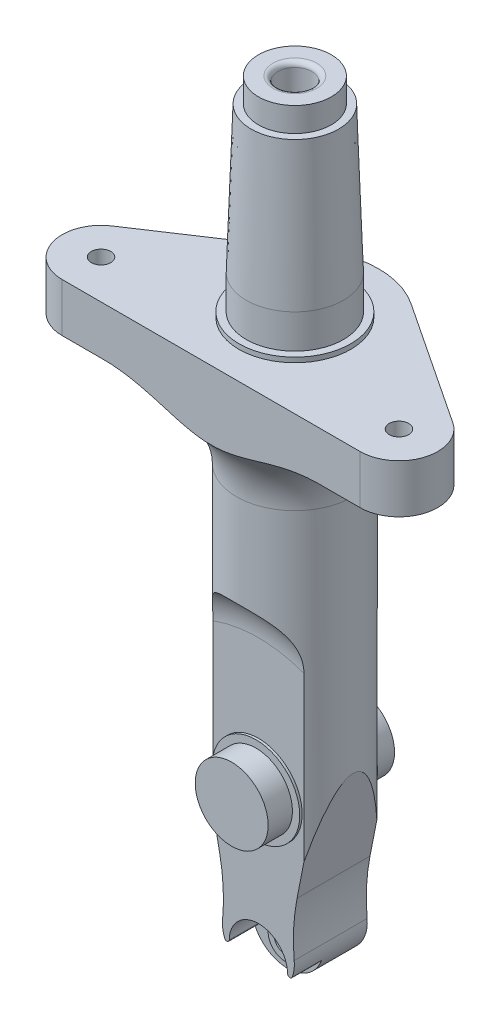
SolidWorks part; units mm, degrees
ref_plane "Front Plane" through (0, 0, 0) normal (0, 0, 1) x (1, 0, 0)
ref_plane "Top Plane" through (0, 0, 0) normal (0, 1, 0) x (1, 0, 0)
ref_plane "Right Plane" through (0, 0, 0) normal (1, 0, 0) x (0, 0, -1)
sketch "Sketch1" plane through (0, 0, 0) normal (1, 0, 0) x (0, 0, -1)
  line L0 (0, 0) -> (-12, 0)
  line L1 (-12, 0) -> (-12, 88.2723)
  line L2 (-12, 88.2723) -> (0, 88.2723)
  line L3 (0, 88.2723) -> (0, 0)
  dimension "D1" = 12
revolve "Revolve1" add sketch "Sketch1" angle 360 about L3
sketch "Sketch2" plane through (0, 0, 0) normal (1, 0, 0) x (0, 0, -1)
  line L0 (0, 0) -> (0, 42.6195) construction
  line L5 (-12, 88.2723) -> (-12, 0) construction
  line L6 (-12, 0) -> (-7.5, 0)
  line L7 (-12, 0) -> (12, 0) construction
  line L8 (-12, 0) -> (-12, 60)
  line L9 (-12, 60) -> (-7.5, 60)
  line L10 (-7.5, 0) -> (-7.5, 60)
  line L11 (7.5, 0) -> (7.5, 60)
  line L12 (12, 60) -> (7.5, 60)
  line L13 (12, 0) -> (12, 60)
  line L14 (12, 0) -> (7.5, 0)
  dimension "D1" = 7.5
  dimension "D2" = 60
extrude "Cut-Extrude1" cut sketch "Sketch2" against normal through all both and the other way through all
sketch "Sketch3" plane through (0, 0, 7.5) normal (0, 0, 1) x (1, 0, 0)
  line L0 (-9.3675, 0) -> (9.3675, 0) construction
  line L1 (0, 5) -> (0, 0) construction
  line L2 (-12, 40) -> (12, 40) construction
  line L3 (-12, 88.2723) -> (-12, 0) construction
  line L4 (12, 0) -> (12, 88.2723) construction
  line L5 (-12, 40) -> (-4.9055, 4.0324)
  line L6 (12, 40) -> (4.9055, 4.0324)
  line L7 (-12, 40) -> (-12, 0)
  line L9 (12, 0) -> (12, 40)
  line L10 (-12, 0) -> (-12, -1)
  line L11 (-12, -1) -> (12, -1)
  line L12 (12, -1) -> (12, 0)
  arc A0 (-4.9055, 4.0324) -> (4.9055, 4.0324) centre (0, 5) ccw
  dimension "D1" = 10
  dimension "D2" = 40
  dimension "D3" = 1
extrude "Cut-Extrude2" cut sketch "Sketch3" against normal through all both and the other way through all
sketch "Sketch12" plane through (0, 0, 7.5) normal (0, 0, 1) x (1, 0, 0)
  circle A0 centre (0, 7.3939) radius 7.3939
extrude "Boss-Extrude4" add sketch "Sketch12" against normal up to surface (15 mm away) up to face at (0, 29.5567, -7.5)
fillet "Fillet2" radius 40 2 edges at (-6.3241, 11.2247, 0) (6.3241, 11.2247, 0)
sketch "Sketch4" plane through (0, 0, 7.5) normal (0, 0, 1) x (1, 0, 0)
  line L0 (0, 5) -> (0, 0) construction
  circle A0 centre (0, 5) radius 6
  dimension "D1" = 12
  dimension "D2" = 5
extrude "Cut-Extrude3" cut sketch "Sketch4" against normal blind 6
sketch "Sketch5" plane through (0, 0, 1.5) normal (0, 0, 1) x (1, 0, 0)
  line L0 (0, 5) -> (0, 0) construction
  circle A0 centre (0, 5) radius 2.25
  dimension "D1" = 4.5
  dimension "D2" = 5
extrude "Cut-Extrude4" cut sketch "Sketch5" against normal through all
sketch "Sketch6" plane through (0, 0, 0) normal (0, 0, 1) x (1, 0, 0)
  line L0 (0, 35) -> (0, 5) construction
  circle A0 centre (0, 35) radius 7.5
  dimension "D1" = 15
  dimension "D2" = 30
extrude "Boss-Extrude1" add sketch "Sketch6" along normal mid plane 26
sketch "Sketch7" plane through (0, 0, 0) normal (1, 0, 0) x (0, 0, -1)
  line L0 (-43.1434, 61.9274) -> (-20.4641, 61.9274) construction
  line L5 (0, 88.2723) -> (0, 0) construction
  line L6 (12, 88.2723) -> (-12, 88.2723) construction
  line L7 (-7.5, 26.6538) -> (-7.5, 60) construction
  line L8 (-7.5, 61.9274) -> (-7.5, 51.9274)
  line L11 (-13, 35) -> (13, 35) construction
  line L12 (-13, 42.5) -> (-13, 27.5) construction
  line L13 (13, 27.5) -> (13, 42.5) construction
  line L16 (-7.5, 51.9274) -> (-17.5, 51.9274)
  line L17 (7.5, 51.9274) -> (17.5, 51.9274)
  line L18 (7.5, 61.9274) -> (7.5, 51.9274)
  arc A2 (-7.5, 61.9274) -> (-17.5, 51.9274) centre (-17.5, 61.9274) ccw
  arc A4 (7.5, 61.9274) -> (17.5, 51.9274) centre (17.5, 61.9274) cw
  point P9 (-7.5, 61.9274)
  point P27 (7.5, 61.9274)
  dimension "D1" = 20
revolve "Cut-Revolve1" cut sketch "Sketch7" angle 360 about L11
sketch "Sketch8" plane through (0, 0, 0) normal (1, 0, 0) x (0, 0, -1)
  line L0 (0, 88.2723) -> (0, 25.4203)
  line L1 (12, 88.2723) -> (-12, 88.2723) construction
  arc A0 (0, 25.4203) -> (12.8128, 10.5806) centre (15, 25.4203) ccw
  dimension "D1" = 30
sketch "Sketch9" plane through (0, 88.2723, 0) normal (0, 1, 0) x (1, 0, 0)
  circle A0 centre (0, 0) radius 3.5
  dimension "D1" = 7
sweep "Cut-Sweep1" cut profiles "Sketch9" path "Sketch8"
sketch "Sketch10" plane through (0, 0, 0) normal (0, 0, 1) x (1, 0, 0)
  circle A0 centre (0, 35) radius 9
  dimension "D1" = 18
extrude "Boss-Extrude2" add sketch "Sketch10" along normal mid plane 16
sketch "Sketch11" plane through (0, 0, 1.5) normal (0, 0, 1) x (1, 0, 0)
  circle A0 centre (0, 5) radius 2.25 construction
  circle A1 centre (0, 5) radius 2.25
  circle A2 centre (0, 5) radius 3.5
  dimension "D1" = 7
extrude "Boss-Extrude3" add sketch "Sketch11" along normal blind 0.5
fillet "Fillet1" radius 0.5 2 edges at (5.3569, 2.2975, 4.5) (-5.3569, 2.2975, 4.5)
sketch "Sketch13" plane through (0, 88.2723, 0) normal (0, 1, 0) x (1, 0, 0)
  circle A0 centre (0, 0) radius 3.5 construction
  circle A1 centre (0, 0) radius 12
  circle A2 centre (0, 0) radius 12
  circle A3 centre (0, 0) radius 3.5
  dimension "D1" = 0
extrude "Boss-Extrude5" add sketch "Sketch13" along normal blind 17
sketch "Sketch15" plane through (0, 0, 0) normal (1, 0, 0) x (0, 0, -1)
  line L0 (-13, 35) -> (13, 35) construction
  line L1 (-13, 42.5) -> (-13, 27.5) construction
  line L2 (13, 27.5) -> (13, 42.5) construction
  line L3 (0, 88.826) -> (0, 43.2314) construction
  line L4 (12, 105.2723) -> (-12, 105.2723) construction
  line L5 (0, 105.2723) -> (-40, 105.2723)
  line L6 (0, 105.2723) -> (0, 123.2723)
  line L8 (-40, 105.2723) -> (-40, 115.2723)
  line L9 (-11.5, 115.2723) -> (-40, 115.2723)
  line L12 (0, 123.2723) -> (-10, 123.2723)
  line L13 (-10, 116.2723) -> (-10, 123.2723)
  line L16 (-10, 116.2723) -> (-11.5, 116.2723)
  line L17 (-11.5, 115.2723) -> (-11.5, 116.2723)
  dimension "D1" = 40
  dimension "D2" = 10
  dimension "D3" = 10
  dimension "D4" = 7
  dimension "D5" = 1
  dimension "D6" = 1.5
revolve "Revolve2" add sketch "Sketch15" angle 360 about L3
fillet "Fillet3" radius 16 1 edges at (0, 105.2723, 12)
sketch "Sketch16" plane through (0, 115.2723, 0) normal (0, 1, 0) x (1, 0, 0)
  line L0 (-30.6386, -9.2345) -> (0, 0) construction
  line L1 (0, 0) -> (38.2982, -11.5432) construction
  line L2 (0, 0) -> (0, -40) construction
  line L3 (-30.6386, -17.2345) -> (30.6386, -17.2345)
  line L4 (-35.0594, -2.567) -> (-9.5239, 14.364)
  line L5 (9.5239, 14.364) -> (35.0594, -2.567)
  arc A0 (-35.0594, -2.567) -> (-30.6386, -17.2345) centre (-30.6386, -9.2345) ccw
  circle A1 centre (0, 0) radius 40 construction
  arc A2 (30.6386, -17.2345) -> (35.0594, -2.567) centre (30.6386, -9.2345) ccw
  arc A4 (9.5239, 14.364) -> (-9.5239, 14.364) centre (0, 0) ccw
  circle A6 centre (0, 0) radius 77.6503
  circle A9 centre (0, 0) radius 17.2345 construction
  dimension "D2" = 8
  dimension "D1" = 34.4691
extrude "Cut-Extrude5" cut sketch "Sketch16" against normal blind 22
sketch "Sketch17" plane through (0, 115.2723, 0) normal (0, 1, 0) x (1, 0, 0)
  circle A0 centre (-30.6386, -9.2345) radius 2
  circle A1 centre (30.6386, -9.2345) radius 2
  dimension "D1" = 4
extrude "Cut-Extrude6" cut sketch "Sketch17" against normal blind 22
sketch "Sketch19" plane through (0, 0, 0) normal (0, 0, 1) x (1, 0, 0)
  line L0 (0, 123.2723) -> (0, 158.2723) construction
  line L1 (10, 123.2723) -> (-10, 123.2723) construction
  line L2 (-10, 123.2723) -> (-9, 153.2723)
  line L3 (0, 158.2723) -> (-7.5, 158.2723)
  line L6 (-7.5, 158.2723) -> (-7.5, 153.2723)
  line L7 (-9, 153.2723) -> (-7.5, 153.2723)
  line L8 (0, 158.2723) -> (0, 123.2723)
  line L9 (0, 123.2723) -> (-10, 123.2723)
  dimension "D1" = 5
  dimension "D2" = 7.5
  dimension "D3" = 35
  dimension "D4" = 1.5
revolve "Revolve3" add sketch "Sketch19" angle 360 about L0
sketch "Sketch20" plane through (0, 158.2723, 0) normal (0, 1, 0) x (1, 0, 0)
  circle A0 centre (0, 0) radius 3.5
  dimension "D1" = 7
extrude "Cut-Extrude7" cut sketch "Sketch20" against normal up to surface (132.852 mm away)
fillet "Fillet5" radius 1 1 edges at (-3.5, 158.2723, 0)
